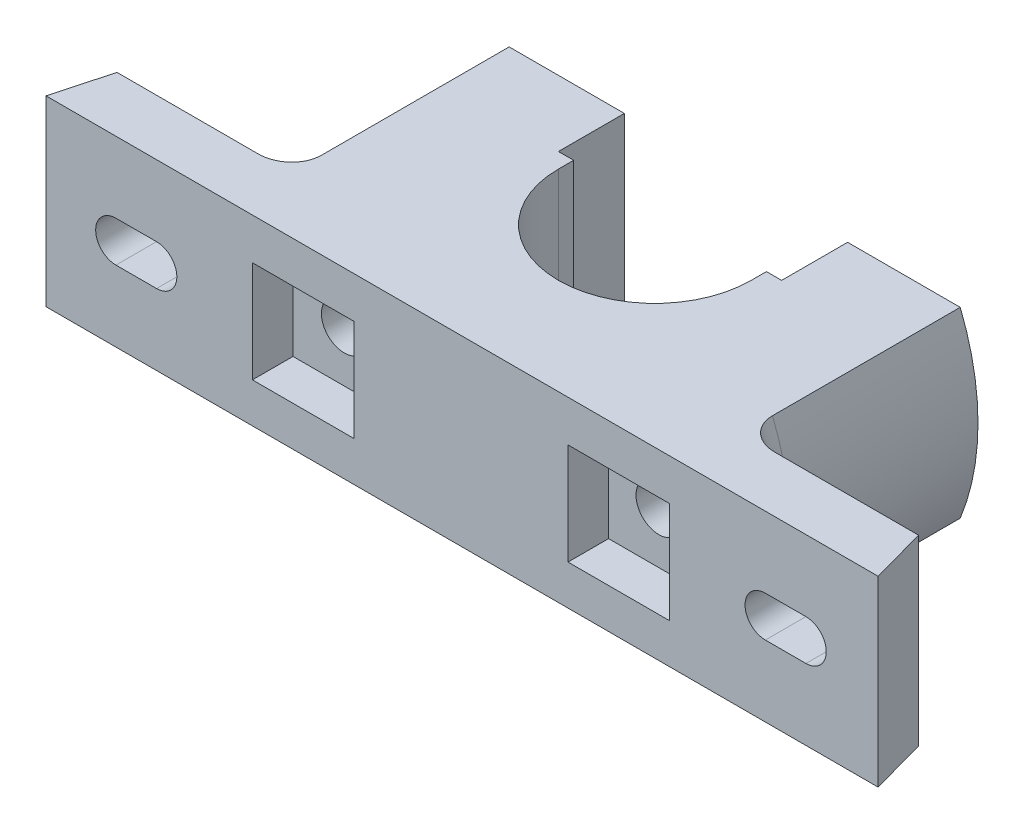
SolidWorks part; units mm, degrees
ref_plane "Front Plane" through (0, 0, 0) normal (0, 0, 1) x (1, 0, 0)
ref_plane "Top Plane" through (0, 0, 0) normal (0, 1, 0) x (1, 0, 0)
ref_plane "Right Plane" through (0, 0, 0) normal (1, 0, 0) x (0, 0, -1)
sketch "Sketch1" plane through (0, 0, 0) normal (0, 1, 0) x (1, 0, 0)
  line L0 (0.2119, -0.0784) -> (139.3244, -0.0784) construction
  line L1 (0.2119, -0.0784) -> (0.2119, 85.4041) construction
  line L2 (19.2119, 37.9216) -> (19.2119, 40.9216)
  line L3 (19.2119, 40.9216) -> (22.2119, 40.9216)
  line L4 (22.2119, 40.9216) -> (22.2119, 53.9216)
  line L5 (22.2119, 53.9216) -> (50.2119, 53.9216)
  line L6 (50.2119, 53.9216) -> (50.2119, 10.9216)
  line L7 (-21.7881, 53.9216) -> (-49.7881, 53.9216)
  line L8 (-21.7881, 40.9216) -> (-21.7881, 53.9216)
  line L9 (-18.7881, 40.9216) -> (-21.7881, 40.9216)
  line L10 (-18.7881, 37.9216) -> (-18.7881, 40.9216)
  line L11 (-81.7881, -0.0784) -> (82.2119, -0.0784)
  line L12 (82.2119, -0.0784) -> (79.2119, 10.9216)
  line L13 (79.2119, 10.9216) -> (50.2119, 10.9216)
  line L14 (-49.7881, 53.9216) -> (-49.7881, 10.9216)
  line L15 (-78.7881, 10.9216) -> (-49.7881, 10.9216)
  line L16 (-81.7881, -0.0784) -> (-78.7881, 10.9216)
  arc A0 (-18.7881, 37.9216) -> (19.2119, 37.9216) centre (0.2119, 37.9216) ccw
  dimension "D1" = 19
  dimension "D2" = 38
  dimension "D13" = 16
  dimension "D3" = 38
  dimension "D4" = 44
  dimension "D5" = 16
  dimension "D6" = 82
  dimension "D7" = 13
  dimension "D8" = 54
  dimension "D9" = 11
  dimension "D10" = 3
  dimension "D11" = 43
  dimension "D12" = 50
extrude "Boss-Extrude1" add sketch "Sketch1" along normal mid plane 36
ref_plane "Plane1" through (0, 0, -53.9216) normal (0, 0, -1) x (-1, 0, 0)
sketch "Sketch3" plane through (0, 0, -53.9216) normal (0, 0, -1) x (-1, 0, 0)
  line L0 (21.7881, 18) -> (49.7881, 18) construction
  line L1 (49.7881, 18) -> (49.7881, -18) construction
  line L2 (21.7881, -18) -> (49.7881, -18) construction
  line L3 (44.4972, 18) -> (49.7881, 18)
  line L4 (49.7881, 18) -> (49.7881, -18)
  line L5 (44.4972, -18) -> (49.7881, -18)
  arc A0 (44.4972, -18) -> (44.4972, 18) centre (0, 0) ccw
  dimension "D1" = 96
extrude "Cut-Extrude2" cut sketch "Sketch3" against normal blind 43 contours A0 L3 L4 L5
fillet "Fillet2" radius 6 1 edges at (-48, 0, -10.9216)
sketch "Sketch4" plane through (0, 0, -53.9216) normal (0, 0, -1) x (-1, 0, 0)
  circle A0 centre (31, 0) radius 4.5
  point P0 (31, 0)
  dimension "D2" = 9
  dimension "D1" = 31
extrude "Cut-Extrude3" cut sketch "Sketch4" against normal through all
sketch "Sketch5" plane through (0, 0, 0) normal (0, 0, 1) x (1, 0, 0)
  line L1 (-21.1, 9.8585) -> (-41.1, 9.8585)
  line L2 (-21.1, 9.8585) -> (-21.1, -10.1415)
  line L3 (-21.1, -10.1415) -> (-41.1, -10.1415)
  line L4 (-41.1, 9.8585) -> (-41.1, -10.1415)
  line L5 (-21.1, 9.8585) -> (-41.1, -10.1415) construction
  line L6 (-21.1, -10.1415) -> (-41.1, 9.8585) construction
  point P0 (-31, 0)
  dimension "D1" = 31
  dimension "D4" = 20
  dimension "D5" = 20
extrude "Cut-Extrude6" cut sketch "Sketch5" along normal mid plane 15.84
sketch "Sketch6" plane through (0, 0, -10.9216) normal (0, 0, -1) x (-1, 0, 0)
  line L0 (60, 0) -> (68, 0) construction
  line L1 (60, 4) -> (68, 4)
  line L2 (60, -4) -> (68, -4)
  arc A0 (60, 4) -> (60, -4) centre (60, 0) ccw
  arc A1 (68, -4) -> (68, 4) centre (68, 0) ccw
  point P2 (64, 0)
  dimension "D1" = 64
  dimension "D2" = 8
extrude "Cut-Extrude7" cut sketch "Sketch6" against normal through all
hole_wizard "Ø6.0mm Dowel Hole1" positions "3DSketch1" profile "Sketch9" hole size "Ø6.0" standard "ANSI Metric"
sketch3d "3DSketch1"
  point P0 (0, 0, -18.9228)
  dimension "D1" = 0
  dimension "D2" = 0
sketch "Sketch9" plane through (0, 0, -18.9228) normal (0, 1, 0) x (-0.9999, 0, -0.0112)
  line L0 (0, 0) -> (0, 7.8026)
  line L1 (0, 7.8026) -> (3, 6)
  line L2 (3, 6) -> (3, 0)
  line L5 (3, 0) -> (0, 0)
  line L10 (0, 7.8026) -> (-3, 6) construction
  line L11 (0, -6.35) -> (0, 107.95) construction
  dimension "Hole Dia." = 6
  dimension "Hole Depth" = 6
  dimension "Drill Angle" = 118
mirror "Mirror3" about plane through (0, 0, 0) normal (1, 0, 0) of "Cut-Extrude6", "Cut-Extrude7", "Cut-Extrude3"
sketch "Sketch10" plane through (0, 0, -53.9216) normal (0, 0, -1) x (-1, 0, 0)
  line L0 (-50.2119, -18) -> (-22.2119, -18) construction
  line L1 (-50.2119, 18) -> (-50.2119, -18) construction
  line L2 (-50.2119, 18) -> (-22.2119, 18) construction
  line L3 (-50.2119, -18) -> (-44.4102, -18)
  line L4 (-50.2119, 18) -> (-50.2119, -18)
  line L5 (-50.2119, 18) -> (-44.4102, 18)
  arc A0 (-44.4102, 18) -> (-44.4102, -18) centre (0.087, 0) ccw
  dimension "D1" = 96
extrude "Cut-Extrude8" cut sketch "Sketch10" against normal blind 43
fillet "Fillet3" radius 6 1 edges at (47.913, 0, -10.9216)
